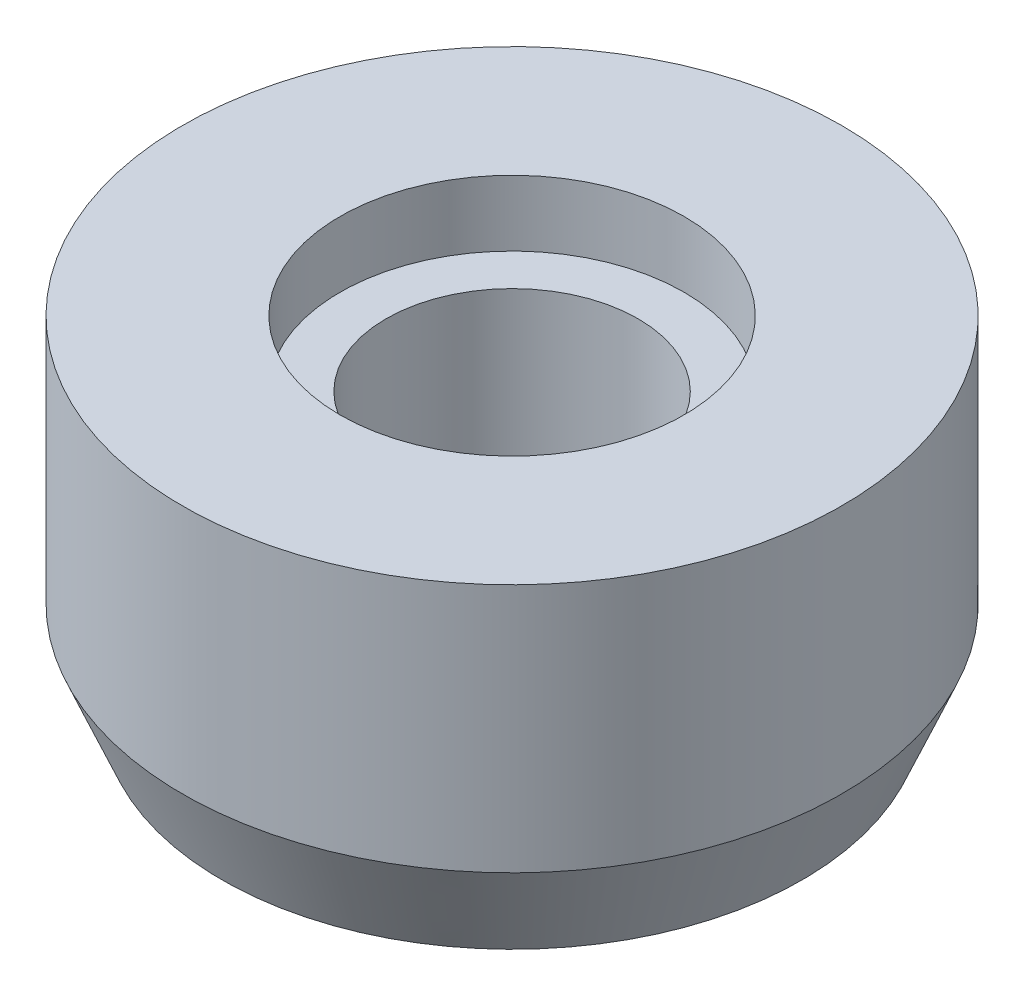
SolidWorks part; units mm, degrees
ref_plane "Front Plane" through (0, 0, 0) normal (0, 0, 1) x (1, 0, 0)
ref_plane "Top Plane" through (0, 0, 0) normal (0, 1, 0) x (1, 0, 0)
ref_plane "Right Plane" through (0, 0, 0) normal (1, 0, 0) x (0, 0, -1)
sketch "Sketch1" plane through (0, 0, 0) normal (0, 0, 1) x (1, 0, 0)
  line L0 (4.8, 0) -> (11.05, 0)
  line L1 (11.05, 0) -> (12.55, 3.5826)
  line L2 (12.55, 3.5826) -> (12.55, 13.0826)
  line L3 (12.55, 13.0826) -> (6.55, 13.0826)
  line L4 (6.55, 13.0826) -> (6.55, 10.5826)
  line L5 (6.55, 10.5826) -> (4.8, 10.5826)
  line L6 (4.8, 10.5826) -> (4.8, 0)
  line L7 (0, 0) -> (0, 16.7536) construction
  dimension "D1" = 4.8
  dimension "D2" = 9.5
  dimension "D3" = 6
  dimension "D4" = 1.5
  dimension "D5" = 7.75
  dimension "D6" = 2.5
  dimension "D7" = 1.75
revolve "Revolve1" add sketch "Sketch1" angle 360 about L7
